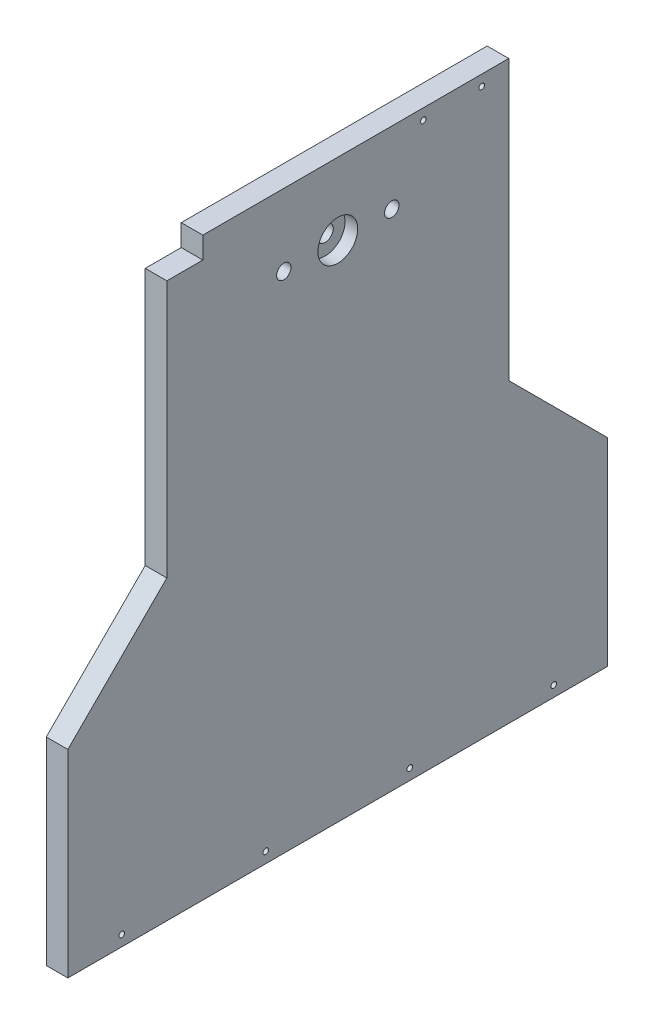
SolidWorks part; units mm, degrees
ref_plane "Front Plane" through (0, 0, 0) normal (0, 0, 1) x (1, 0, 0)
ref_plane "Top Plane" through (0, 0, 0) normal (0, 1, 0) x (1, 0, 0)
ref_plane "Right Plane" through (0, 0, 0) normal (1, 0, 0) x (0, 0, -1)
sketch "Sketch1" plane through (0, 0, 0) normal (1, 0, 0) x (0, 0, -1)
  line L0 (0, 0) -> (0, 320) construction
  line L1 (95, 320) -> (-95, 320)
  line L2 (-95, 320) -> (-95, 165)
  line L3 (-95, 165) -> (-150, 110)
  line L4 (-150, 110) -> (-150, 0)
  line L5 (-150, 0) -> (150, 0)
  line L6 (150, 110) -> (150, 0)
  line L7 (95, 165) -> (150, 110)
  line L8 (95, 320) -> (95, 165)
  dimension "D1" = 320
  dimension "D2" = 225
  dimension "D3" = 150
  dimension "D4" = 155
  dimension "D5" = 110
extrude "Boss-Extrude1" add sketch "Sketch1" along normal blind 12
sketch "Sketch2" plane through (0, 0, 0) normal (-1, 0, 0) x (0, 0, 1)
  line L0 (-95, 165) -> (-95, 320) construction
  line L1 (95, 320) -> (95, 165) construction
  line L2 (150, 0) -> (-150, 0) construction
  circle A0 centre (30, 280) radius 4
  circle A1 centre (-30, 280) radius 4
  dimension "D1" = 8
  dimension "D3" = 8
  dimension "D4" = 280
  dimension "D5" = 65
  dimension "D6" = 65
  dimension "280" = 280
extrude "Cut-Extrude1" cut sketch "Sketch2" against normal through all
sketch "Sketch3" plane through (0, 0, 0) normal (-1, 0, 0) x (0, 0, 1)
  line L0 (150, 0) -> (-150, 0) construction
  circle A0 centre (0, 280) radius 4.5
  dimension "D1" = 9
  dimension "D2" = 280
extrude "Cut-Extrude2" cut sketch "Sketch3" against normal through all
sketch "Sketch4" plane through (12, 0, 0) normal (1, 0, 0) x (0, 0, -1)
  circle A0 centre (0, 280) radius 11.05
  dimension "D1" = 22.1
extrude "Cut-Extrude3" cut sketch "Sketch4" against normal blind 7
sketch "Sketch5" plane through (12, 0, 0) normal (1, 0, 0) x (0, 0, -1)
  line L1 (-95, 320) -> (-75, 320)
  line L2 (-95, 320) -> (-95, 308)
  line L3 (-95, 308) -> (-75, 308)
  line L4 (-75, 320) -> (-75, 308)
  dimension "D1" = 20
  dimension "D2" = 12
extrude "Cut-Extrude4" cut sketch "Sketch5" against normal through all
sketch "Sketch6" plane through (12, 0, 0) normal (1, 0, 0) x (0, 0, -1)
  line L0 (-150, 0) -> (150, 0) construction
  line L1 (150, 0) -> (150, 110) construction
  line L2 (-150, 110) -> (-150, 0) construction
  line L3 (95, 165) -> (95, 320) construction
  line L4 (95, 320) -> (-75, 320) construction
  circle A0 centre (-120, 6) radius 1.55
  circle A1 centre (-40, 6) radius 1.55
  circle A2 centre (40, 6) radius 1.55
  circle A3 centre (120, 6) radius 1.55
  circle A4 centre (80, 314) radius 1.55
  circle A5 centre (47.5, 314) radius 1.55
  dimension "D1" = 3.1
  dimension "D2" = 3.1
  dimension "D3" = 3.1
  dimension "D4" = 3.1
  dimension "D13" = 3.1
  dimension "D14" = 3.1
  dimension "D5" = 6
  dimension "D6" = 6
  dimension "D7" = 6
  dimension "D8" = 6
  dimension "D9" = 30
  dimension "D10" = 30
  dimension "D11" = 80
  dimension "D12" = 160
  dimension "D15" = 15
  dimension "D16" = 47.5
  dimension "D17" = 6
  dimension "D18" = 6
extrude "Cut-Extrude5" cut sketch "Sketch6" against normal through all
